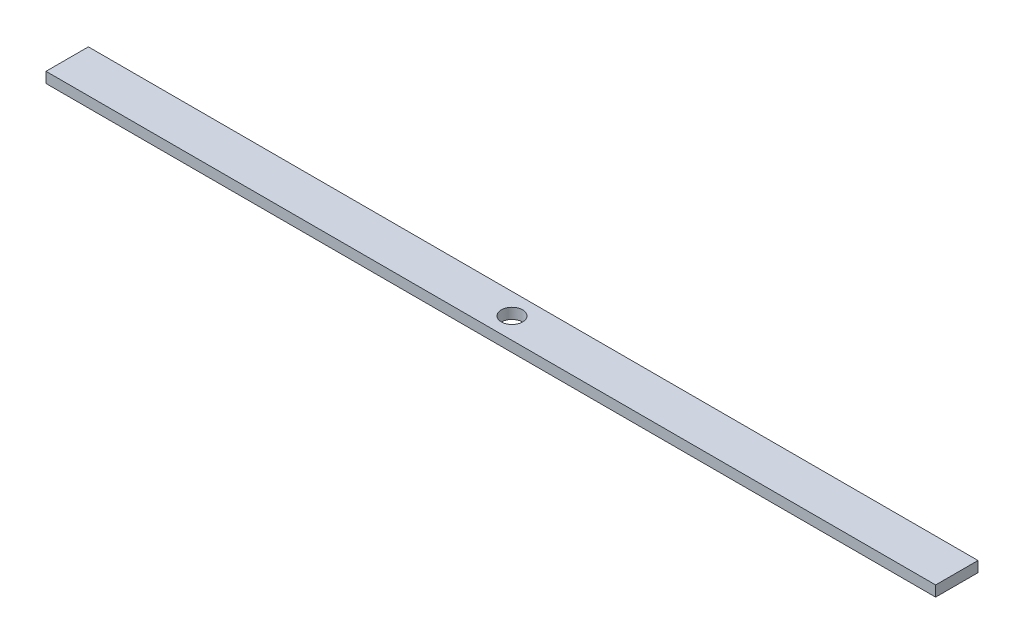
SolidWorks part; units mm, degrees
material "6061-T6 (SS)"
ref_plane "Front Plane" through (0, 0, 0) normal (0, 0, 1) x (1, 0, 0)
ref_plane "Top Plane" through (0, 0, 0) normal (0, 1, 0) x (1, 0, 0)
ref_plane "Right Plane" through (0, 0, 0) normal (1, 0, 0) x (0, 0, -1)
sketch "Sketch1" plane through (0, 0, 0) normal (0, 1, 0) x (1, 0, 0)
  line L1 (-266.7, 12.7) -> (266.7, 12.7)
  line L2 (-266.7, 12.7) -> (-266.7, -12.7)
  line L3 (-266.7, -12.7) -> (266.7, -12.7)
  line L4 (266.7, 12.7) -> (266.7, -12.7)
  line L5 (-266.7, 12.7) -> (266.7, -12.7) construction
  line L6 (-266.7, -12.7) -> (266.7, 12.7) construction
  circle A0 centre (0, 0) radius 6.35
  point P0 (0, 0)
  dimension "D1" = 533.4
  dimension "D2" = 25.4
extrude "Boss-Extrude1" add sketch "Sketch1" along normal blind 6.35
